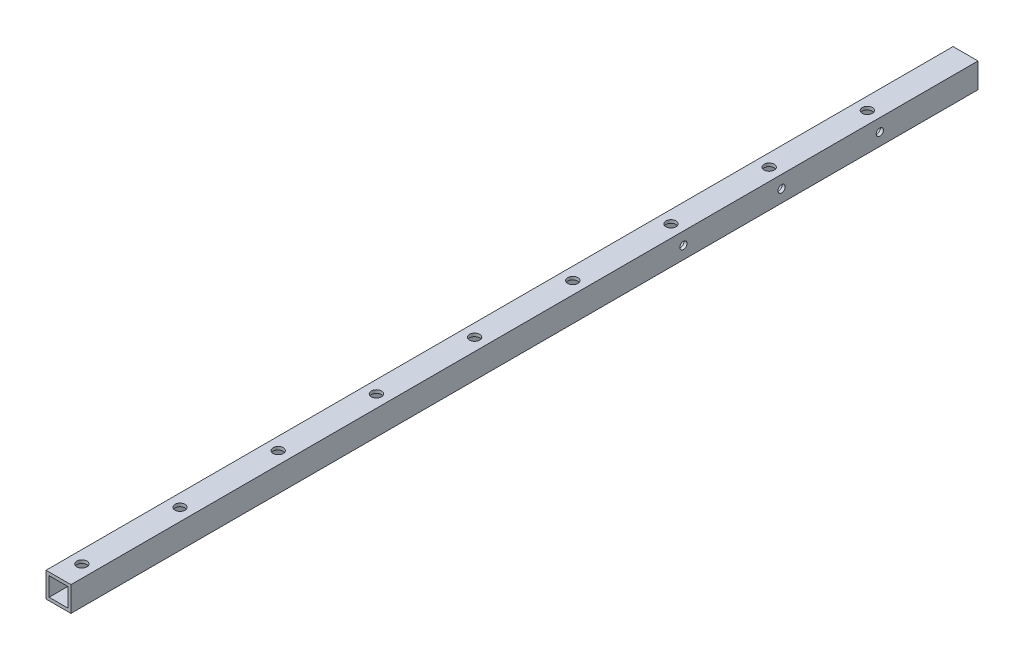
SolidWorks part; units mm, degrees
material "6061-T6 (SS)"
ref_plane "Front Plane" through (0, 0, 0) normal (0, 0, 1) x (1, 0, 0)
ref_plane "Top Plane" through (0, 0, 0) normal (0, 1, 0) x (1, 0, 0)
ref_plane "Right Plane" through (0, 0, 0) normal (1, 0, 0) x (0, 0, -1)
sketch "Sketch1" plane through (0, 0, 0) normal (0, 0, 1) x (1, 0, 0)
  line L0 (13.97, 0) -> (-13.97, 0) construction
  line L1 (-12.7, 12.7) -> (12.7, 12.7)
  line L2 (-12.7, 12.7) -> (-12.7, -12.7)
  line L3 (-12.7, -12.7) -> (12.7, -12.7)
  line L4 (12.7, 12.7) -> (12.7, -12.7)
  line L5 (0, -13.97) -> (0, 13.97) construction
  line L7 (-9.525, 9.525) -> (9.525, 9.525)
  line L8 (-9.525, 9.525) -> (-9.525, -9.525)
  line L9 (-9.525, -9.525) -> (9.525, -9.525)
  line L10 (9.525, 9.525) -> (9.525, -9.525)
  dimension "D1" = 25.4
  dimension "D2" = 25.4
  dimension "D3" = 12.7
  dimension "D4" = 12.7
  dimension "D5" = 3.175
  dimension "D6" = 3.175
  dimension "D7" = 3.175
  dimension "D8" = 3.175
extrude "Boss-Extrude1" add sketch "Sketch1" along normal blind 923.8
sketch "Sketch2" plane through (0, 12.7, 0) normal (0, 1, 0) x (1, 0, 0)
  line L0 (-55, 0) -> (55, 0) construction
  circle A0 centre (0, -100) radius 5.175
  circle A1 centre (0, -200) radius 5.175
  circle A2 centre (0, -300) radius 5.175
  circle A3 centre (0, -400) radius 5.175
  circle A4 centre (0, -500) radius 5.175
  circle A5 centre (0, -600) radius 5.175
  circle A6 centre (0, -700) radius 5.175
  circle A7 centre (0, -800) radius 5.175
  circle A8 centre (0, -900) radius 5.175
  dimension "D1" = 10.35
  dimension "D2" = 100
  dimension "D3" = 9
extrude "Cut-Extrude1" cut sketch "Sketch2" against normal through all
sketch "Sketch3" plane through (-12.7, 0, 0) normal (-1, 0, 0) x (0, 0, 1)
  line L0 (0, -55) -> (0, 55) construction
  circle A0 centre (100, 0) radius 3.675
  circle A1 centre (200, 0) radius 3.675
  circle A2 centre (300, 0) radius 3.675
  dimension "D1" = 7.35
  dimension "D2" = 100
  dimension "D3" = 3
extrude "Cut-Extrude2" cut sketch "Sketch3" against normal through all
